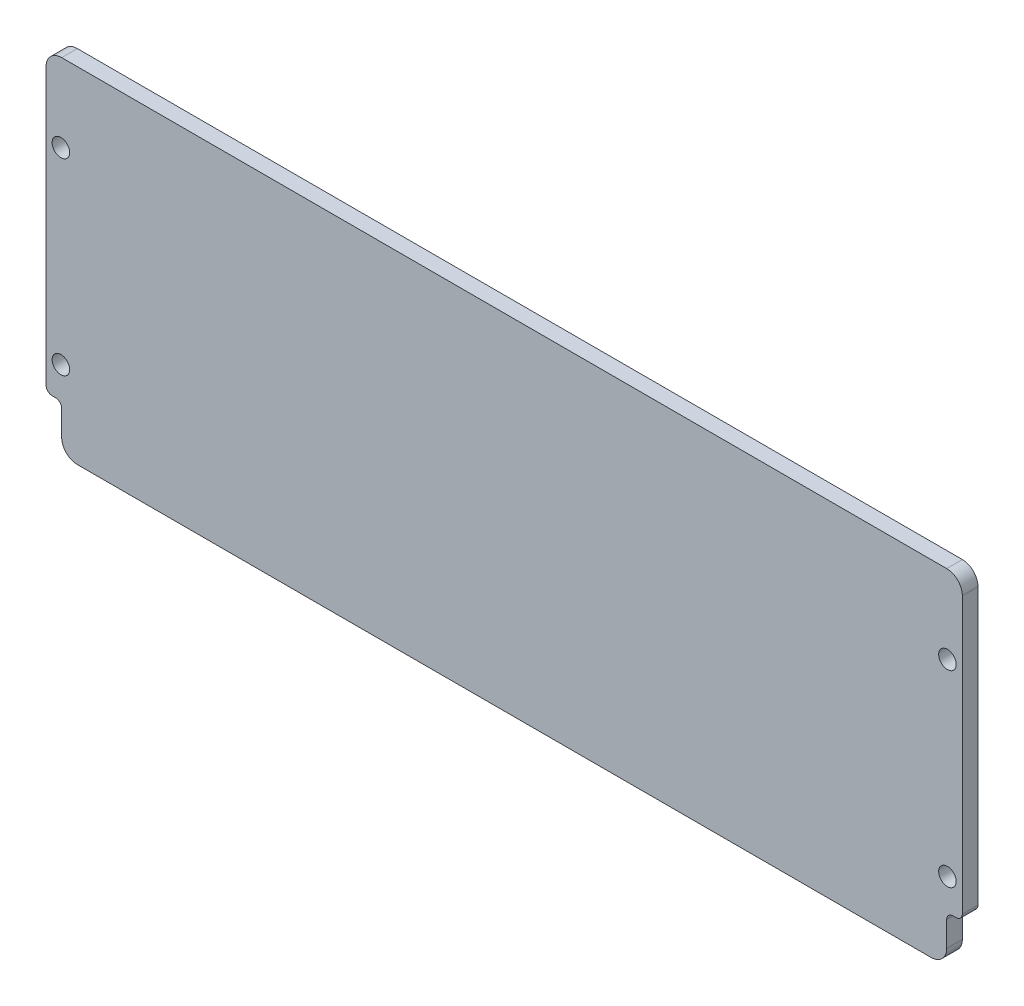
SolidWorks part; units mm, degrees
material "Polyester Resin"
ref_plane "Front Plane" through (0, 0, 0) normal (0, 0, 1) x (1, 0, 0)
ref_plane "Top Plane" through (0, 0, 0) normal (0, 1, 0) x (1, 0, 0)
ref_plane "Right Plane" through (0, 0, 0) normal (1, 0, 0) x (0, 0, -1)
sketch "Sketch1" plane through (0, 0, 0) normal (0, 0, 1) x (1, 0, 0)
  line L2 (-185.7375, 133.35) -> (-185.7375, 21.59)
  line L3 (-173.0375, 0) -> (173.0375, 0)
  line L4 (185.7375, 133.35) -> (185.7375, 21.59)
  line L5 (-179.3875, 139.7) -> (179.3875, 139.7)
  line L8 (0, -55) -> (0, 55) construction
  line L9 (-183.1975, 19.05) -> (-181.9275, 19.05)
  line L10 (-179.3875, 16.51) -> (-179.3875, 6.35)
  line L11 (183.1975, 19.05) -> (181.9275, 19.05)
  line L12 (179.3875, 16.51) -> (179.3875, 6.35)
  line L13 (-179.3875, 139.7) -> (-185.7375, 139.7) construction
  line L14 (-185.7375, 139.7) -> (-185.7375, 133.35) construction
  line L15 (-179.705, 107.95) -> (-179.705, 31.75) construction
  line L16 (179.705, 107.95) -> (179.705, 31.75) construction
  arc A8 (185.7375, 133.35) -> (179.3875, 139.7) centre (179.3875, 133.35) ccw
  arc A9 (-185.7375, 133.35) -> (-179.3875, 139.7) centre (-179.3875, 133.35) cw
  arc A10 (183.1975, 19.05) -> (185.7375, 21.59) centre (183.1975, 21.59) ccw
  arc A11 (181.9275, 19.05) -> (179.3875, 16.51) centre (181.9275, 16.51) ccw
  arc A12 (-181.9275, 19.05) -> (-179.3875, 16.51) centre (-181.9275, 16.51) cw
  arc A13 (-183.1975, 19.05) -> (-185.7375, 21.59) centre (-183.1975, 21.59) cw
  arc A14 (173.0375, 0) -> (179.3875, 6.35) centre (173.0375, 6.35) ccw
  arc A15 (-179.3875, 6.35) -> (-173.0375, 0) centre (-173.0375, 6.35) ccw
  circle A16 centre (-179.705, 31.75) radius 3.556
  circle A17 centre (-179.705, 107.95) radius 3.556
  circle A18 centre (179.705, 107.95) radius 3.556
  circle A19 centre (179.705, 31.75) radius 3.556
  point P22 (185.7375, 19.05)
  point P23 (185.7375, 0)
  point P26 (185.7375, 139.7)
  point P29 (-185.7375, 139.7)
  point P35 (179.3875, 19.05)
  point P38 (-179.3875, 19.05)
  point P41 (-185.7375, 19.05)
  point P44 (179.3875, 0)
  point P47 (-179.3875, 0)
  dimension "D3" = 6.35
  dimension "D4" = 7.112
  dimension "D6" = 6.0325
  dimension "D7" = 6.35
  dimension "D10" = 2.54
  dimension "D11" = 31.75
  dimension "D5" = 76.2
  dimension "D1" = 371.475
  dimension "D2" = 139.7
  dimension "D8" = 19.05
  dimension "D9" = 6.35
extrude "Boss-Extrude1" add sketch "Sketch1" along normal blind 6.35
sketch "Sketch4" plane through (0, 0, 6.35) normal (0, 0, 1) x (1, 0, 0)
  line L0 (-179.705, 31.75) -> (175.5775, 31.75) construction
  line L1 (-175.5775, 69.85) -> (175.5775, 69.85) construction
  line L2 (0, -3.4925) -> (0, 3.4925) construction
  line L3 (-43.9941, 69.85) -> (-65.9911, 107.95) construction
  line L4 (-65.9911, 107.95) -> (-109.9852, 107.95) construction
  line L5 (-109.9852, 107.95) -> (-131.9823, 69.85) construction
  line L6 (-131.9823, 69.85) -> (-109.9852, 31.75) construction
  line L7 (-109.9852, 31.75) -> (-65.9911, 31.75) construction
  line L8 (-179.705, 107.95) -> (175.5775, 107.95) construction
  line L9 (-65.9911, 31.75) -> (-43.9941, 69.85) construction
  line L10 (-43.9941, 69.85) -> (-21.997, 31.75) construction
  line L11 (-21.997, 31.75) -> (21.997, 31.75) construction
  line L12 (21.997, 31.75) -> (43.9941, 69.85) construction
  line L13 (43.9941, 69.85) -> (21.997, 107.95) construction
  line L14 (21.997, 107.95) -> (-21.997, 107.95) construction
  line L15 (-21.997, 107.95) -> (-43.9941, 69.85) construction
  line L16 (-175.5775, 129.54) -> (-175.5775, 27.5085)
  line L17 (-169.2275, 16.51) -> (-169.2275, 10.16)
  line L18 (-169.2275, 10.16) -> (169.2275, 10.16)
  line L19 (169.2275, 10.16) -> (169.2275, 16.51)
  line L20 (175.5775, 27.5085) -> (175.5775, 129.54)
  line L21 (175.5775, 129.54) -> (-175.5775, 129.54)
  line L22 (-175.5775, 129.54) -> (-175.5775, 27.5085)
  line L23 (-169.2275, 16.51) -> (-169.2275, 10.16)
  line L24 (-169.2275, 10.16) -> (169.2275, 10.16)
  line L25 (169.2275, 10.16) -> (169.2275, 16.51)
  line L26 (175.5775, 27.5085) -> (175.5775, 129.54)
  line L27 (175.5775, 129.54) -> (-175.5775, 129.54)
  line L28 (43.9941, 69.85) -> (65.9911, 31.75) construction
  line L29 (65.9911, 31.75) -> (109.9852, 31.75) construction
  line L30 (109.9852, 31.75) -> (131.9823, 69.85) construction
  line L31 (131.9823, 69.85) -> (109.9852, 107.95) construction
  line L32 (109.9852, 107.95) -> (65.9911, 107.95) construction
  line L33 (65.9911, 107.95) -> (43.9941, 69.85) construction
  line L34 (131.9823, 69.85) -> (153.9793, 31.75) construction
  line L35 (153.9793, 31.75) -> (197.9734, 31.75) construction
  line L36 (197.9734, 31.75) -> (219.9705, 69.85) construction
  line L37 (219.9705, 69.85) -> (197.9734, 107.95) construction
  line L38 (197.9734, 107.95) -> (153.9793, 107.95) construction
  line L39 (153.9793, 107.95) -> (131.9823, 69.85) construction
  line L40 (-131.9823, 69.85) -> (-153.9793, 107.95) construction
  line L41 (-153.9793, 107.95) -> (-197.9734, 107.95) construction
  line L42 (-197.9734, 107.95) -> (-219.9705, 69.85) construction
  line L43 (-219.9705, 69.85) -> (-197.9734, 31.75) construction
  line L44 (-197.9734, 31.75) -> (-153.9793, 31.75) construction
  line L45 (-153.9793, 31.75) -> (-131.9823, 69.85) construction
  line L46 (-43.9941, -6.35) -> (-65.9911, 31.75) construction
  line L47 (-65.9911, 31.75) -> (-109.9852, 31.75) construction
  line L48 (-109.9852, 31.75) -> (-131.9823, -6.35) construction
  line L49 (-131.9823, -6.35) -> (-109.9852, -44.45) construction
  line L50 (-109.9852, -44.45) -> (-65.9911, -44.45) construction
  line L51 (-65.9911, -44.45) -> (-43.9941, -6.35) construction
  line L52 (-131.9823, -6.35) -> (-153.9793, 31.75) construction
  line L53 (-153.9793, 31.75) -> (-197.9734, 31.75) construction
  line L54 (-197.9734, 31.75) -> (-219.9705, -6.35) construction
  line L55 (-219.9705, -6.35) -> (-197.9734, -44.45) construction
  line L56 (-197.9734, -44.45) -> (-153.9793, -44.45) construction
  line L57 (-153.9793, -44.45) -> (-131.9823, -6.35) construction
  line L58 (-43.9941, -6.35) -> (-21.997, -44.45) construction
  line L59 (-21.997, -44.45) -> (21.997, -44.45) construction
  line L60 (21.997, -44.45) -> (43.9941, -6.35) construction
  line L61 (43.9941, -6.35) -> (21.997, 31.75) construction
  line L62 (21.997, 31.75) -> (-21.997, 31.75) construction
  line L63 (-21.997, 31.75) -> (-43.9941, -6.35) construction
  line L64 (43.9941, -6.35) -> (65.9911, -44.45) construction
  line L65 (65.9911, -44.45) -> (109.9852, -44.45) construction
  line L66 (109.9852, -44.45) -> (131.9823, -6.35) construction
  line L67 (131.9823, -6.35) -> (109.9852, 31.75) construction
  line L68 (109.9852, 31.75) -> (65.9911, 31.75) construction
  line L69 (65.9911, 31.75) -> (43.9941, -6.35) construction
  line L70 (131.9823, -6.35) -> (153.9793, -44.45) construction
  line L71 (153.9793, -44.45) -> (197.9734, -44.45) construction
  line L72 (197.9734, -44.45) -> (219.9705, -6.35) construction
  line L73 (219.9705, -6.35) -> (197.9734, 31.75) construction
  line L74 (197.9734, 31.75) -> (153.9793, 31.75) construction
  line L75 (153.9793, 31.75) -> (131.9823, -6.35) construction
  line L76 (-43.9941, 69.85) -> (-65.9911, 107.95) construction
  line L77 (-65.9911, 107.95) -> (-109.9852, 107.95) construction
  line L78 (-109.9852, 107.95) -> (-131.9823, 69.85) construction
  line L79 (-131.9823, 69.85) -> (-109.9852, 31.75) construction
  line L80 (-109.9852, 31.75) -> (-65.9911, 31.75) construction
  line L81 (-65.9911, 31.75) -> (-43.9941, 69.85) construction
  line L82 (-131.9823, 69.85) -> (-153.9793, 107.95) construction
  line L83 (-153.9793, 107.95) -> (-197.9734, 107.95) construction
  line L84 (-197.9734, 107.95) -> (-219.9705, 69.85) construction
  line L85 (-219.9705, 69.85) -> (-197.9734, 31.75) construction
  line L86 (-197.9734, 31.75) -> (-153.9793, 31.75) construction
  line L87 (-153.9793, 31.75) -> (-131.9823, 69.85) construction
  line L88 (-43.9941, 69.85) -> (-21.997, 31.75) construction
  line L89 (-21.997, 31.75) -> (21.997, 31.75) construction
  line L90 (21.997, 31.75) -> (43.9941, 69.85) construction
  line L91 (43.9941, 69.85) -> (21.997, 107.95) construction
  line L92 (21.997, 107.95) -> (-21.997, 107.95) construction
  line L93 (-21.997, 107.95) -> (-43.9941, 69.85) construction
  line L94 (43.9941, 69.85) -> (65.9911, 31.75) construction
  line L95 (65.9911, 31.75) -> (109.9852, 31.75) construction
  line L96 (109.9852, 31.75) -> (131.9823, 69.85) construction
  line L97 (131.9823, 69.85) -> (109.9852, 107.95) construction
  line L98 (109.9852, 107.95) -> (65.9911, 107.95) construction
  line L99 (65.9911, 107.95) -> (43.9941, 69.85) construction
  line L100 (131.9823, 69.85) -> (153.9793, 31.75) construction
  line L101 (153.9793, 31.75) -> (197.9734, 31.75) construction
  line L102 (197.9734, 31.75) -> (219.9705, 69.85) construction
  line L103 (219.9705, 69.85) -> (197.9734, 107.95) construction
  line L104 (197.9734, 107.95) -> (153.9793, 107.95) construction
  line L105 (153.9793, 107.95) -> (131.9823, 69.85) construction
  line L106 (-43.9941, 146.05) -> (-65.9911, 184.15) construction
  line L107 (-65.9911, 184.15) -> (-109.9852, 184.15) construction
  line L108 (-109.9852, 184.15) -> (-131.9823, 146.05) construction
  line L109 (-131.9823, 146.05) -> (-109.9852, 107.95) construction
  line L110 (-109.9852, 107.95) -> (-65.9911, 107.95) construction
  line L111 (-65.9911, 107.95) -> (-43.9941, 146.05) construction
  line L112 (-131.9823, 146.05) -> (-153.9793, 184.15) construction
  line L113 (-153.9793, 184.15) -> (-197.9734, 184.15) construction
  line L114 (-197.9734, 184.15) -> (-219.9705, 146.05) construction
  line L115 (-219.9705, 146.05) -> (-197.9734, 107.95) construction
  line L116 (-197.9734, 107.95) -> (-153.9793, 107.95) construction
  line L117 (-153.9793, 107.95) -> (-131.9823, 146.05) construction
  line L118 (-43.9941, 146.05) -> (-21.997, 107.95) construction
  line L119 (-21.997, 107.95) -> (21.997, 107.95) construction
  line L120 (21.997, 107.95) -> (43.9941, 146.05) construction
  line L121 (43.9941, 146.05) -> (21.997, 184.15) construction
  line L122 (21.997, 184.15) -> (-21.997, 184.15) construction
  line L123 (-21.997, 184.15) -> (-43.9941, 146.05) construction
  line L124 (43.9941, 146.05) -> (65.9911, 107.95) construction
  line L125 (65.9911, 107.95) -> (109.9852, 107.95) construction
  line L126 (109.9852, 107.95) -> (131.9823, 146.05) construction
  line L127 (131.9823, 146.05) -> (109.9852, 184.15) construction
  line L128 (109.9852, 184.15) -> (65.9911, 184.15) construction
  line L129 (65.9911, 184.15) -> (43.9941, 146.05) construction
  line L130 (131.9823, 146.05) -> (153.9793, 107.95) construction
  line L131 (153.9793, 107.95) -> (197.9734, 107.95) construction
  line L132 (197.9734, 107.95) -> (219.9705, 146.05) construction
  line L133 (219.9705, 146.05) -> (197.9734, 184.15) construction
  line L134 (197.9734, 184.15) -> (153.9793, 184.15) construction
  line L135 (153.9793, 184.15) -> (131.9823, 146.05) construction
  line L136 (-197.9734, 184.15) -> (-65.9911, -44.45) construction
  line L137 (-109.9852, 184.15) -> (21.997, -44.45) construction
  line L138 (-21.997, 184.15) -> (109.9852, -44.45) construction
  line L139 (65.9911, 184.15) -> (197.9734, -44.45) construction
  line L140 (153.9793, 184.15) -> (197.9734, 107.95) construction
  line L141 (-197.9734, 31.75) -> (-153.9793, -44.45) construction
  line L142 (-197.9734, 107.95) -> (-153.9793, 184.15) construction
  line L143 (-197.9734, 107.95) -> (-153.9793, 31.75) construction
  line L144 (-109.9852, 107.95) -> (-65.9911, 31.75) construction
  line L145 (-21.997, 107.95) -> (21.997, 31.75) construction
  line L146 (65.9911, 107.95) -> (109.9852, 31.75) construction
  line L147 (153.9793, 107.95) -> (197.9734, 31.75) construction
  line L148 (-197.9734, 31.75) -> (-153.9793, 107.95) construction
  line L149 (-21.997, 31.75) -> (21.997, 107.95) construction
  line L150 (-197.9734, -44.45) -> (-65.9911, 184.15) construction
  line L151 (-109.9852, 31.75) -> (-65.9911, 107.95) construction
  line L152 (-109.9852, -44.45) -> (21.997, 184.15) construction
  line L153 (-21.997, -44.45) -> (109.9852, 184.15) construction
  line L154 (65.9911, -44.45) -> (197.9734, 184.15) construction
  line L155 (65.9911, 31.75) -> (109.9852, 107.95) construction
  line L156 (153.9793, 31.75) -> (197.9734, 107.95) construction
  line L157 (153.9793, -44.45) -> (197.9734, 31.75) construction
  line L158 (-179.705, 102.87) -> (175.5775, 102.87)
  line L159 (-179.705, 26.67) -> (175.5775, 26.67)
  line L160 (-127.5829, 72.39) -> (-149.5799, 110.49)
  line L161 (-149.5799, 29.21) -> (-127.5829, 67.31)
  line L162 (-136.3817, 67.31) -> (-114.3846, 29.21)
  line L163 (-114.3846, 110.49) -> (-136.3817, 72.39)
  line L164 (-193.574, -46.99) -> (-61.5917, 181.61)
  line L165 (-202.3728, 181.61) -> (-70.3905, -46.99)
  line L166 (-105.5858, -46.99) -> (26.3965, 181.61)
  line L167 (-114.3846, 181.61) -> (17.5976, -46.99)
  line L168 (-17.5976, -46.99) -> (114.3846, 181.61)
  line L169 (61.5917, 181.61) -> (193.574, -46.99)
  line L170 (70.3905, -46.99) -> (202.3728, 181.61)
  line L171 (-26.3965, 181.61) -> (105.5858, -46.99)
  line L172 (-179.705, 113.03) -> (175.5775, 113.03)
  line L173 (-179.705, 36.83) -> (175.5775, 36.83)
  line L174 (-136.3817, 67.31) -> (-158.3787, 105.41)
  line L175 (-158.3787, 34.29) -> (-136.3817, 72.39)
  line L176 (-127.5829, 72.39) -> (-105.5858, 34.29)
  line L177 (-105.5858, 105.41) -> (-127.5829, 67.31)
  line L178 (-202.3728, -41.91) -> (-70.3905, 186.69)
  line L179 (-193.574, 186.69) -> (-61.5917, -41.91)
  line L180 (-114.3846, -41.91) -> (17.5976, 186.69)
  line L181 (-105.5858, 186.69) -> (26.3965, -41.91)
  line L182 (-26.3965, -41.91) -> (105.5858, 186.69)
  line L183 (70.3905, 186.69) -> (202.3728, -41.91)
  line L184 (61.5917, -41.91) -> (193.574, 186.69)
  line L185 (-17.5976, 186.69) -> (114.3846, -41.91)
  line L186 (-151.7796, 106.68) -> (-131.9823, 140.97)
  line L187 (-131.9823, 140.97) -> (-112.1849, 106.68)
  line L188 (-112.1849, 106.68) -> (-68.1908, 30.48)
  line L189 (-195.7737, 30.48) -> (-151.7796, 106.68)
  line L190 (-175.5775, 67.31) -> (175.5775, 67.31)
  line L191 (-200.1731, 106.68) -> (-156.179, 30.48)
  line L192 (-112.1849, 33.02) -> (-131.9823, -1.27)
  line L193 (-131.9823, -1.27) -> (-151.7796, 33.02)
  line L194 (-107.7855, 30.48) -> (-63.7914, 106.68)
  line L195 (-63.7914, 106.68) -> (-43.9941, 140.97)
  line L196 (-43.9941, 140.97) -> (-24.1967, 106.68)
  line L197 (-24.1967, 33.02) -> (-43.9941, -1.27)
  line L198 (-43.9941, -1.27) -> (-63.7914, 33.02)
  line L199 (-19.7973, 30.48) -> (24.1967, 106.68)
  line L200 (24.1967, 106.68) -> (43.9941, 140.97)
  line L201 (43.9941, 140.97) -> (63.7914, 106.68)
  line L202 (-24.1967, 106.68) -> (19.7973, 30.48)
  line L203 (63.7914, 33.02) -> (43.9941, -1.27)
  line L204 (43.9941, -1.27) -> (24.1967, 33.02)
  line L205 (68.1908, 30.48) -> (112.1849, 106.68)
  line L206 (112.1849, 106.68) -> (131.9823, 140.97)
  line L207 (131.9823, 140.97) -> (151.7796, 106.68)
  line L208 (151.7796, 106.68) -> (195.7737, 30.48)
  line L209 (63.7914, 106.68) -> (107.7855, 30.48)
  line L210 (131.9823, -11.43) -> (107.7855, 30.48)
  line L211 (156.179, 30.48) -> (131.9823, -11.43)
  line L212 (156.179, 30.48) -> (200.1731, 106.68)
  line L213 (-156.179, 109.22) -> (-131.9823, 151.13)
  line L214 (-131.9823, 151.13) -> (-107.7855, 109.22)
  line L215 (-107.7855, 109.22) -> (-63.7914, 33.02)
  line L216 (-200.1731, 33.02) -> (-156.179, 109.22)
  line L217 (-175.5775, 72.39) -> (175.5775, 72.39)
  line L218 (-195.7737, 109.22) -> (-151.7796, 33.02)
  line L219 (-107.7855, 30.48) -> (-131.9823, -11.43)
  line L220 (-131.9823, -11.43) -> (-156.179, 30.48)
  line L221 (-112.1849, 33.02) -> (-68.1908, 109.22)
  line L222 (-68.1908, 109.22) -> (-43.9941, 151.13)
  line L223 (-43.9941, 151.13) -> (-19.7973, 109.22)
  line L224 (-19.7973, 30.48) -> (-43.9941, -11.43)
  line L225 (-43.9941, -11.43) -> (-68.1908, 30.48)
  line L226 (-24.1967, 33.02) -> (19.7973, 109.22)
  line L227 (19.7973, 109.22) -> (43.9941, 151.13)
  line L228 (43.9941, 151.13) -> (68.1908, 109.22)
  line L229 (-19.7973, 109.22) -> (24.1967, 33.02)
  line L230 (68.1908, 30.48) -> (43.9941, -11.43)
  line L231 (43.9941, -11.43) -> (19.7973, 30.48)
  line L232 (63.7914, 33.02) -> (107.7855, 109.22)
  line L233 (107.7855, 109.22) -> (131.9823, 151.13)
  line L234 (131.9823, 151.13) -> (156.179, 109.22)
  line L235 (156.179, 109.22) -> (200.1731, 33.02)
  line L236 (68.1908, 109.22) -> (112.1849, 33.02)
  line L237 (131.9823, -1.27) -> (112.1849, 33.02)
  line L238 (151.7796, 33.02) -> (131.9823, -1.27)
  line L239 (151.7796, 33.02) -> (195.7737, 109.22)
  circle A0 centre (-179.705, 107.95) radius 3.556 construction
  circle A1 centre (-87.9882, 69.85) radius 38.1 construction
  circle A2 centre (0, 69.85) radius 38.1 construction
  circle A3 centre (87.9882, 69.85) radius 38.1 construction
  circle A4 centre (175.9764, 69.85) radius 38.1 construction
  circle A5 centre (-175.9764, 69.85) radius 38.1 construction
  arc A16 (-169.2275, 16.51) -> (-175.5775, 27.5085) centre (-181.9275, 16.51) ccw
  arc A17 (175.5775, 27.5085) -> (169.2275, 16.51) centre (181.9275, 16.51) ccw
  arc A18 (-169.2275, 16.51) -> (-175.5775, 27.5085) centre (-181.9275, 16.51) ccw
  arc A19 (175.5775, 27.5085) -> (169.2275, 16.51) centre (181.9275, 16.51) ccw
  dimension "D2" = 38.1
  dimension "D5" = 38.1
  dimension "D6" = 5.08
  dimension "D1" = 10.16
  dimension "D7" = 5.08
  dimension "D8" = 2.54
  dimension "D9" = 2.54
  dimension "D3" = 2
  dimension "D4" = 2
extrude "Cut-Extrude2" [suppressed] cut sketch "Sketch4" against normal through all contours L22 L172 L165 L27 | L22 L216 L158 | A18 L23 L178 L159 | L190 L218 L178 | L24 L220 L164 | L193 L24 L192 L159 | L164 L173 L162 | L179 L221 L190 | L177 L217 L188 | L163 L158 L160 | L187 L27 L186 L172 | L27 L214 L178 | L215 L221 L158 | L194 L217 L167 | L190 L215 L180 | L194 L173 L188 | L24 L180 L159 L179 | L165 L219 L24 | L198 L24 L197 L159 | L24 L225 L166 | L166 L173 L167 | L24 L182 L159 L181 | L167 L224 L24 | L202 L199 L173 | L181 L226 L190 | L158 L229 L226 | L166 L217 L202 | L158 L181 L180 | L196 L27 L195 L172 | L181 L222 L27 | L185 L227 L27 | L201 L27 L200 L172 | L158 L185 L182 | L199 L217 L171 | L190 L229 L182 | L168 L173 L171 | L204 L24 L203 L159 | L24 L231 L168 | L171 L230 L24 | L209 L205 L173 | L185 L232 L190 | L168 L217 L209 | L189 L217 L174 | L164 L172 L167 L27 | L166 L172 L171 L27 | L190 L236 L184 | L205 L217 L169 | L158 L236 L232 | L207 L27 L206 L172 | L183 L184 L158 | L170 L217 L208 | L158 L235 L26 | L183 L239 L190 | L170 L173 L169 | L238 L159 L237 L24 | L169 L211 L24 | L212 L173 L26 | L168 L172 L169 L27 | L159 L185 L24 L184 | L24 L210 L170 | L170 L172 L26 L27 | L27 L234 L184 | L183 L233 L27 | L27 L228 L182 | L27 L223 L180 | L179 L213 L27 | L191 L22 L173 | A19 L159 L183 L25
fillet "Fillet1" [suppressed] radius 1.905
